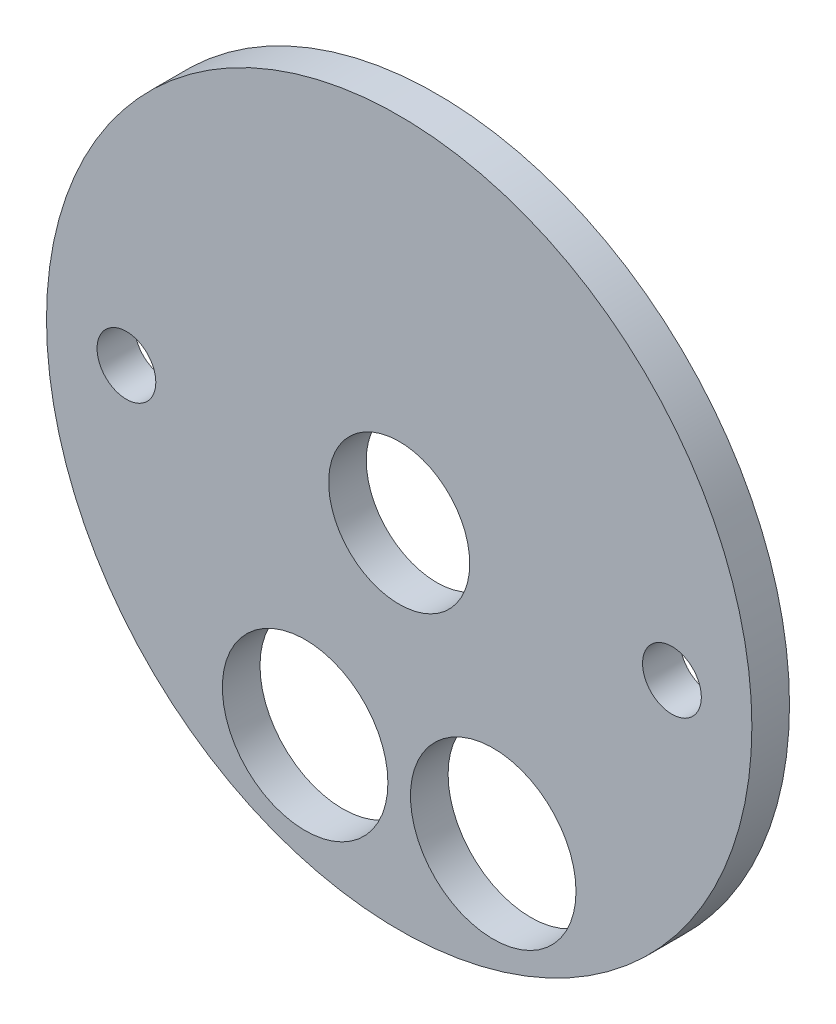
SolidWorks part; units mm, degrees
ref_plane "Front Plane" through (0, 0, 0) normal (0, 0, 1) x (1, 0, 0)
ref_plane "Top Plane" through (0, 0, 0) normal (0, 1, 0) x (1, 0, 0)
ref_plane "Right Plane" through (0, 0, 0) normal (1, 0, 0) x (0, 0, -1)
sketch "Sketch1" plane through (0, 0, 0) normal (0, 0, 1) x (1, 0, 0)
  circle A0 centre (0, 0) radius 49.5046
  dimension "D1" = 99.0092
extrude "Boss-Extrude1" add sketch "Sketch1" along normal blind 5.08
sketch "Sketch2" plane through (0, 0, 5.08) normal (0, 0, 1) x (1, 0, 0)
  circle A0 centre (0, 0) radius 47.625
  dimension "D1" = 95.25
extrude "Boss-Extrude2" add sketch "Sketch2" along normal blind 5.08
sketch "Sketch3" plane through (0, 0, 10.16) normal (0, 0, 1) x (1, 0, 0)
  circle A0 centre (-12.7, -31.1668) radius 11.176
  circle A1 centre (12.7, -31.1668) radius 11.176
  circle A2 centre (-12.7, -31.1668) radius 12.7 construction
  circle A3 centre (-12.7, -31.1668) radius 13.97 construction
  circle A4 centre (12.7, -31.1668) radius 12.7 construction
  circle A5 centre (12.7, -31.1668) radius 13.97 construction
  circle A6 centre (0, 0) radius 47.625 construction
  circle A7 centre (0, 0) radius 47.625 construction
  circle A8 centre (-36.83, 0) radius 3.9688
  circle A9 centre (36.83, 0) radius 3.9687
  circle A10 centre (0, 0) radius 9.525
  dimension "D1" = 27.94
  dimension "D2" = 25.4
  dimension "D3" = 22.352
  dimension "D4" = 7.9375
  dimension "D5" = 7.9375
  dimension "D8" = 19.05
  dimension "D6" = 73.66
  dimension "D7" = 36.83
extrude "Cut-Extrude1" cut sketch "Sketch3" against normal through all
sketch "Sketch7" plane through (0, 0, 0) normal (0, 0, -1) x (-1, 0, 0)
  circle A0 centre (0, 0) radius 65.4214
extrude "Cut-Extrude3" cut sketch "Sketch7" against normal blind 5.08
